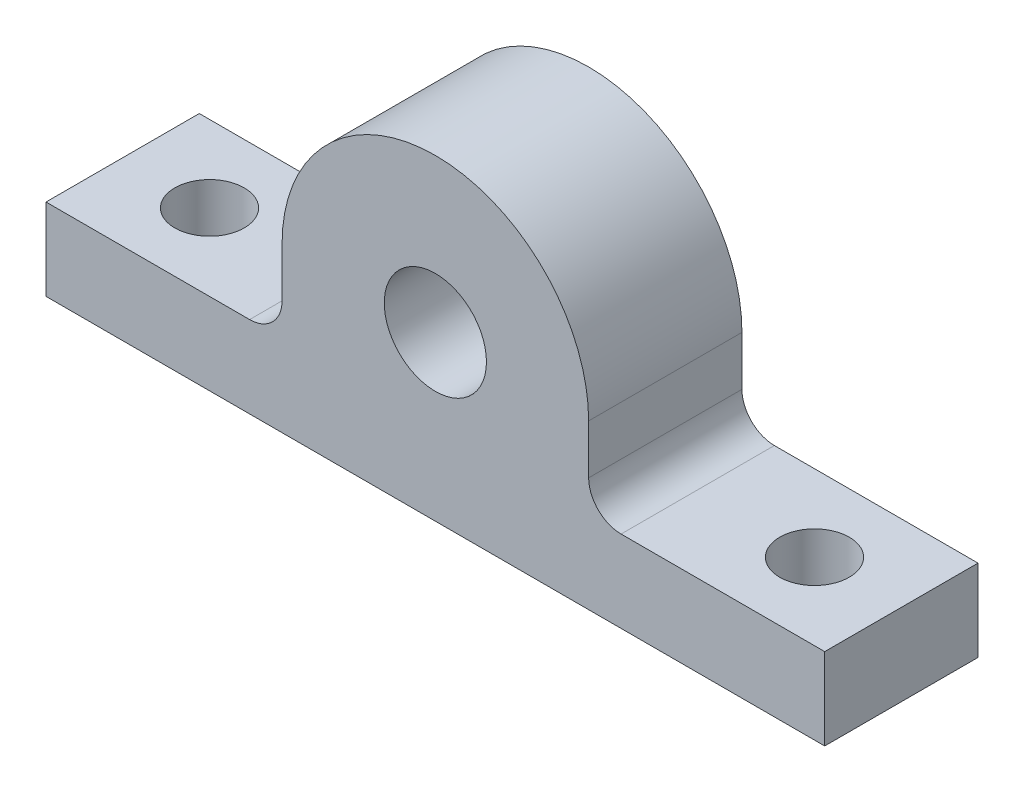
SolidWorks part; units mm, degrees
ref_plane "Front Plane" through (0, 0, 0) normal (0, 0, 1) x (1, 0, 0)
ref_plane "Top Plane" through (0, 0, 0) normal (0, 1, 0) x (1, 0, 0)
ref_plane "Right Plane" through (0, 0, 0) normal (1, 0, 0) x (0, 0, -1)
sketch "Sketch1" plane through (0, 0, 0) normal (0, 0, 1) x (1, 0, 0)
  line L1 (-38.1, -4) -> (38.1, -4)
  line L2 (-38.1, -4) -> (-38.1, 4)
  line L3 (-38.1, 4) -> (38.1, 4)
  line L4 (38.1, -4) -> (38.1, 4)
  line L5 (-38.1, -4) -> (38.1, 4) construction
  line L6 (-38.1, 4) -> (38.1, -4) construction
  line L7 (-15, 4) -> (15, 4)
  line L8 (-15, 4) -> (-15, 12)
  line L9 (-15, 12) -> (15, 12)
  line L10 (15, 4) -> (15, 12)
  line L11 (-15, 4) -> (15, 12) construction
  line L12 (-15, 12) -> (15, 4) construction
  arc A0 (-15, 12) -> (15, 12) centre (0, 12) cw
  circle A1 centre (0, 12) radius 5
  point P0 (0, 0)
  point P6 (0, 8)
  dimension "D4" = 10
  dimension "D1" = 76.2
  dimension "D2" = 8
  dimension "D3" = 8
  dimension "D5" = 30
extrude "Boss-Extrude1" add sketch "Sketch1" along normal blind 15 contours A1 L9 A0 | A1 L9 L8 L3 L10 | L1 L4 L3 L2
sketch "Sketch2" plane through (0, 4, 0) normal (0, 1, 0) x (1, 0, 0)
  line L0 (-38.1, -15) -> (-38.1, 0) construction
  line L1 (38.1, -15) -> (38.1, 0) construction
  point P0 (-29.6, -7.5)
  point P1 (29.6, -7.5)
  point P4 (38.1, -7.5)
  dimension "D1" = 8.5
  dimension "D2" = 8.5
fillet "Fillet1" radius 3.175 2 edges at (-15, 4, 7.5) (15, 4, 7.5)
hole_wizard "Tap Drill for M8x1.25 Tap1" positions "Sketch4" profile "Sketch3" hole size "M8x1.25" standard "ANSI Metric"
sketch "Sketch4" plane through (0, 4, 0) normal (0, 1, 0) x (1, 0, 0)
  point P0 (29.6, -7.5)
  point P3 (-29.6, -7.5)
sketch "Sketch3" plane through (29.6, 4, 7.5) normal (1, 0, 0) x (0, 0, 1)
  line L0 (0, 0) -> (0, 22.0429)
  line L1 (0, 22.0429) -> (3.4, 20)
  line L2 (3.4, 20) -> (3.4, 0)
  line L5 (3.4, 0) -> (0, 0)
  line L10 (0, 22.0429) -> (-3.4, 20) construction
  line L11 (0, -6.35) -> (0, 107.95) construction
  dimension "Hole Dia." = 6.8
  dimension "Hole Depth" = 20
  dimension "Drill Angle" = 118
sketch "Sketch5" plane through (0, 4, 0) normal (0, 1, 0) x (1, 0, 0)
  line L0 (0, 0) -> (0, -15) construction
  line L1 (-15, -15) -> (15, -15) construction
